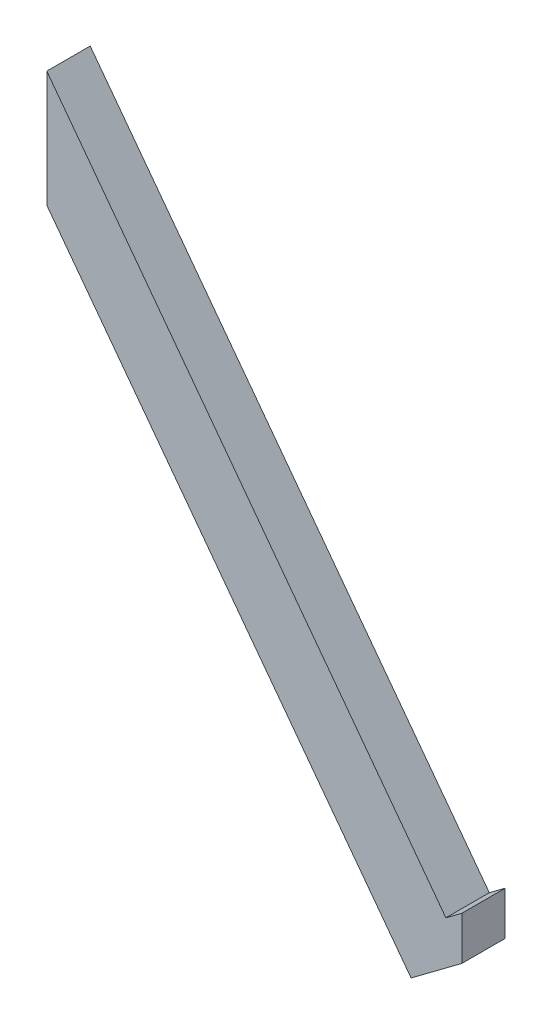
SolidWorks part; units mm, degrees
ref_plane "Alzado" through (0, 0, 0) normal (0, 0, 1) x (1, 0, 0)
ref_plane "Planta" through (0, 0, 0) normal (0, 1, 0) x (1, 0, 0)
ref_plane "Vista lateral" through (0, 0, 0) normal (1, 0, 0) x (0, 0, -1)
sketch "Croquis1" plane through (0, 0, 0) normal (0, 0, 1) x (1, 0, 0)
  line L0 (-48.4511, 38.3968) -> (-2.5236, -23.0179)
  line L1 (-2.5236, -23.0179) -> (-0.6939, -21.6496)
  line L2 (-0.6939, -21.6496) -> (-0.6939, -26.6561)
  line L3 (-0.6939, -26.6561) -> (-6.5291, -31.0198)
  line L4 (-6.5291, -31.0198) -> (-48.4511, 25.0386)
  line L5 (-48.4511, 25.0386) -> (-48.4511, 38.3968)
  dimension "D1" = 70
  dimension "D2" = 8
extrude "Saliente-Extruir1" add sketch "Croquis1" along normal blind 5
